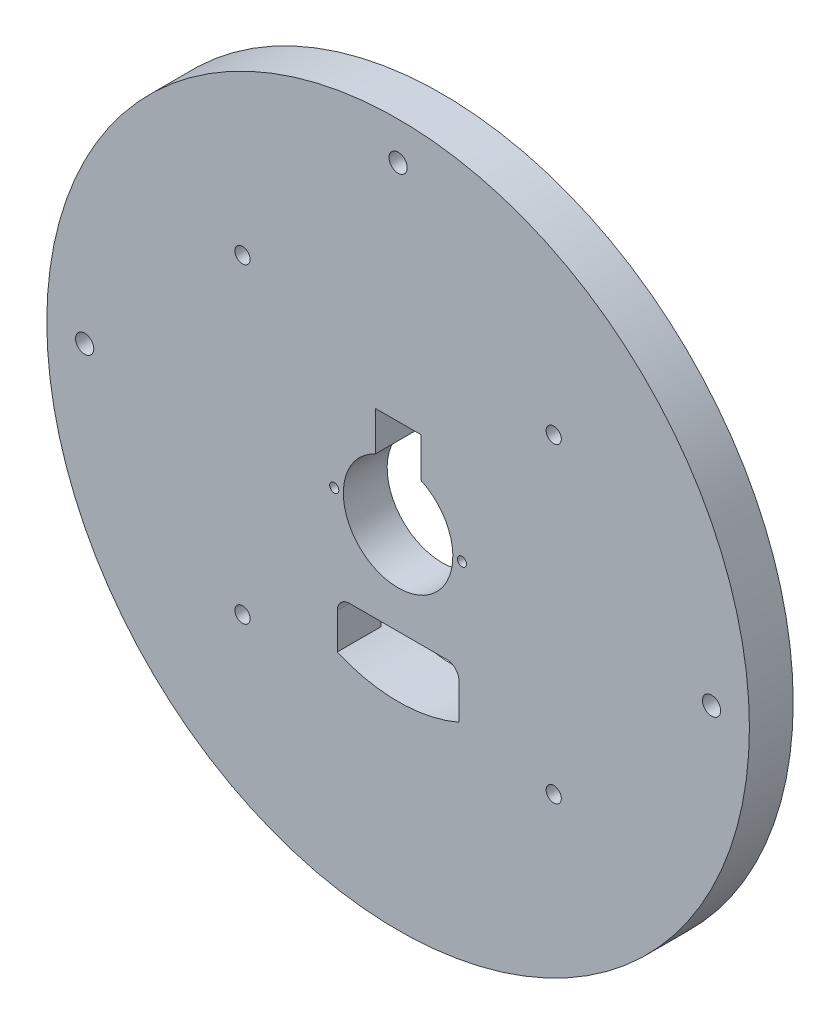
SolidWorks part; units mm, degrees
ref_plane "Front Plane" through (0, 0, 0) normal (0, 0, 1) x (1, 0, 0)
ref_plane "Top Plane" through (0, 0, 0) normal (0, 1, 0) x (1, 0, 0)
ref_plane "Right Plane" through (0, 0, 0) normal (1, 0, 0) x (0, 0, -1)
sketch "motorMount" plane through (0, 0, 0) normal (0, 0, 1) x (1, 0, 0)
  arc A26 (-115.3023, 6.7544) -> (-115.3023, -6.7544) centre (0, 0) ccw
  arc A27 (-115.3023, -6.7544) -> (115.3023, -6.7544) centre (0, 0) ccw
  arc A28 (115.3023, -6.7544) -> (115.3023, 6.7544) centre (0, 0) ccw
  arc A29 (115.3023, 6.7544) -> (-115.3023, 6.7544) centre (0, 0) ccw
  arc A30 (-115.3023, 6.7544) -> (-115.3023, -6.7544) centre (0, 0) ccw
  arc A31 (-115.3023, -6.7544) -> (115.3023, -6.7544) centre (0, 0) ccw
  arc A32 (115.3023, -6.7544) -> (115.3023, 6.7544) centre (0, 0) ccw
  arc A37 (115.3023, 6.7544) -> (-115.3023, 6.7544) centre (0, 0) ccw
  dimension "motorMountOffset" = 30
extrude "Boss-Extrude1" add sketch "motorMount" along normal blind 14.4
sketch "motorMountLockRings" plane through (0, 0, 0) normal (0, 0, -1) x (-1, 0, 0)
  line L0 (-55.2743, 5.1) -> (-55.1648, 5.1)
  line L1 (-55.2743, -5.1) -> (-55.1648, -5.1)
  line L2 (85.3537, 5.1) -> (85.4479, 5.1)
  line L5 (85.3537, -5.1) -> (85.4479, -5.1)
  line L14 (55.1648, 5.1) -> (55.2743, 5.1)
  line L15 (55.1648, -5.1) -> (55.2743, -5.1)
  line L16 (55.2743, 5.1) -> (85.3537, 5.1)
  line L17 (55.2743, 5.1) -> (85.3537, 5.1)
  line L18 (-85.3537, -5.1) -> (-85.4479, -5.1)
  line L19 (55.2743, -5.1) -> (85.3537, -5.1)
  line L20 (55.2743, -5.1) -> (85.3537, -5.1)
  line L21 (-85.3537, 5.1) -> (-85.4479, 5.1)
  line L22 (-85.3537, 5.1) -> (-55.2743, 5.1)
  line L23 (-85.3537, 5.1) -> (-55.2743, 5.1)
  line L25 (-85.3537, -5.1) -> (-55.2743, -5.1)
  line L26 (-85.3537, -5.1) -> (-55.2743, -5.1)
  circle A7 centre (0, 0) radius 50.4
  circle A16 centre (0, 0) radius 50.4
  arc A26 (90.4449, -5.2982) -> (90.4449, 5.2982) centre (0, 0) ccw
  arc A27 (55.1747, 4.991) -> (-55.1747, 4.991) centre (0, 0) ccw
  arc A28 (-90.4449, -5.2982) -> (90.4449, -5.2982) centre (0, 0) ccw
  arc A29 (-90.4449, 5.2982) -> (-90.4449, -5.2982) centre (0, 0) ccw
  arc A30 (55.1648, 5.1) -> (-55.1648, 5.1) centre (0, 0) ccw
  arc A31 (90.4449, 5.2982) -> (-90.4449, 5.2982) centre (0, 0) ccw
  arc A32 (-55.1747, -4.991) -> (55.1747, -4.991) centre (0, 0) ccw
  arc A33 (-55.1648, -5.1) -> (55.1648, -5.1) centre (0, 0) ccw
  arc A34 (90.4449, -5.2982) -> (90.4449, 5.2982) centre (0, 0) ccw
  arc A35 (-90.4449, -5.2982) -> (90.4449, -5.2982) centre (0, 0) ccw
  arc A36 (-90.4449, 5.2982) -> (-90.4449, -5.2982) centre (0, 0) ccw
  arc A37 (90.4449, 5.2982) -> (-90.4449, 5.2982) centre (0, 0) ccw
  arc A61 (85.4535, -5.0058) -> (85.4535, 5.0058) centre (0, 0) ccw
  arc A62 (-85.4535, -5.0058) -> (85.4535, -5.0058) centre (0, 0) ccw
  arc A63 (-85.4535, 5.0058) -> (-85.4535, -5.0058) centre (0, 0) ccw
  arc A64 (85.4535, 5.0058) -> (-85.4535, 5.0058) centre (0, 0) ccw
  arc A66 (-85.4479, -5.1) -> (85.4479, -5.1) centre (0, 0) ccw
  arc A68 (85.4479, 5.1) -> (-85.4479, 5.1) centre (0, 0) ccw
  dimension "D2" = 0.1
  dimension "D3" = 0.1
  dimension "D1" = 0.1
  dimension "D4" = 0.1
  dimension "D5" = 0.1
  dimension "D6" = 0.1
  dimension "D7" = 0.1
  dimension "D8" = 5.1
  dimension "D9" = 0.1
extrude "Boss-Extrude2" add sketch "motorMountLockRings" along normal blind 5
sketch "motorMountMotorCavity" plane through (0, 0, 0) normal (0, 0, -1) x (-1, 0, 0)
  line L0 (-7.5, 16.3631) -> (-7.5, 29.3631)
  line L1 (-7.5, 29.3631) -> (7.5, 29.3631)
  line L2 (7.5, 29.3631) -> (7.5, 16.3631)
  arc A0 (-7.5, 16.3631) -> (7.5, 16.3631) centre (0, 0) ccw
  dimension "motorDiameter" = 36
  dimension "motorConnectorWidth" = 15
  dimension "motorConnectorLength" = 13
extrude "Cut-Extrude1" cut sketch "motorMountMotorCavity" against normal blind 18.4
sketch "motorMountFaceplateHolePositions" plane through (0, 0, 0) normal (0, 0, -1) x (-1, 0, 0)
  line L0 (0, 0) -> (0, 40.4583) construction
  point P1 (-21, 0)
  point P2 (21, 0)
  dimension "motorFacePlateMountingHoleDistanceBetweenHoles" = 21
sketch "motorMountPelletThroughHole" plane through (0, 0, 0) normal (0, 0, -1) x (-1, 0, 0)
  line L0 (-20, -46.2619) -> (-20, -34.4)
  line L1 (-16, -30.4) -> (16, -30.4)
  line L2 (20, -34.4) -> (20, -46.2619)
  arc A2 (-20, -34.4) -> (-16, -30.4) centre (-16, -34.4) cw
  arc A3 (16, -30.4) -> (20, -34.4) centre (16, -34.4) cw
  circle A5 centre (0, 0) radius 50.4 construction
  arc A6 (-20, -46.2619) -> (20, -46.2619) centre (0, 0) ccw
  point P2 (0, -30.4)
  point P16 (0, -50.4)
  dimension "D1" = 4
  dimension "D4" = 20
  dimension "D3" = 40
extrude "Cut-Extrude2" cut sketch "motorMountPelletThroughHole" against normal through all contours L0 A2 L1 A3 L2 A6
hole_wizard "Ø5.0mm Dowel Hole1" positions "Sketch6" profile "Sketch7" hole size "Ø5.0" standard "ANSI Metric" end condition through all
sketch "Sketch6" plane through (0, 0, -16.7) normal (0, 0, -1) x (-1, 0, 0)
  point P0 (-51.1598, -51.1598)
  point P3 (51.1598, -51.1598)
  point P6 (51.1598, 51.1598)
  point P9 (-51.1598, 51.1598)
sketch "Sketch7" plane through (51.1598, -51.1598, -16.7) normal (1, 0, 0) x (0, 1, 0)
  line L0 (0, 0) -> (0, 31.1)
  line L1 (0, 31.1) -> (2.5, 31.1)
  line L2 (2.5, 31.1) -> (2.5, 0)
  line L3 (2.5, 0) -> (0, 0)
  line L4 (0, -6.35) -> (0, 107.95) construction
  dimension "Thru Hole Dia." = 5
  dimension "Thru Hole Depth" = 31.1
hole_wizard "Ø3.0mm Dowel Hole3" positions "Sketch10" profile "Sketch11" hole size "Ø3.0" standard "ANSI Metric" end condition through all
sketch "Sketch10" plane through (0, 0, 0) normal (0, 0, -1) x (-1, 0, 0)
  point P0 (-21, 0)
  point P3 (21, 0)
sketch "Sketch11" plane through (21, 0, 0) normal (1, 0, 0) x (0, 1, 0)
  line L0 (0, 0) -> (0, 14.4)
  line L1 (0, 14.4) -> (1.5, 14.4)
  line L2 (1.5, 14.4) -> (1.5, 0)
  line L3 (1.5, 0) -> (0, 0)
  line L4 (0, -6.35) -> (0, 107.95) construction
  dimension "Thru Hole Dia." = 3
  dimension "Thru Hole Depth" = 14.4
hole_wizard "Ø6.0mm Dowel Hole4" positions "Sketch12" profile "Sketch13" hole size "Ø6.0" standard "ANSI Metric" end condition through all
sketch "Sketch12" plane through (0, 0, 24.4) normal (0, 0, 1) x (1, 0, 0)
  point P0 (-103.05, 0)
  point P3 (103.05, 0)
  point P6 (0, 103.05)
sketch "Sketch13" plane through (-103.05, 0, 24.4) normal (1, 0, 0) x (0, -1, 0)
  line L0 (0, 0) -> (0, 29.4)
  line L1 (0, 29.4) -> (3, 29.4)
  line L2 (3, 29.4) -> (3, 0)
  line L3 (3, 0) -> (0, 0)
  line L4 (0, -6.35) -> (0, 107.95) construction
  dimension "Thru Hole Dia." = 6
  dimension "Thru Hole Depth" = 29.4
equation "\"D1@Boss-Extrude1\"=\"motorMountHeight\""
equation "\"pelletWidth\"= 13mm'The Width of the pellet to be dispensed"
equation "\"pelletLength\"= 26mm'The length of the pellet to be dispensed"
equation "\"pelletThickness\"= 13mm'The Thickness of the pellet to be dispensed"
equation "\"pelletRadius\"= 10mm'The roundness / radius of the pellet to be dispensed"
equation "\"rotatingPlateDiameter\"= 100mm'the diameter of the rotating plate"
equation "\"rotatingPlateHeight\"= (\"pelletThickness\"*0.9)'The thickness of the rotating plate"
equation "\"rotatingPlateDiameterAllowance\"= 0.5mm'Allowance around the edge of the rotating plate"
equation "\"hopperBaseChamferAngle\"= 60deg'Angle of the chamfer of the Hopper base Toward the plate"
equation "\"hopperBaseLipOverhang\"= 5mm'The overhang amount of the hopper base lip"
equation "\"hopperBaseLipDepth\"= 5mm'The depth of the hopper base's overhang lip"
equation "\"hopperBaseRearNotchHeight\"= 8mm'The height of the rear snap-lock notch on the hopper base"
equation "\"hopperBaseRearNotchWidth\"= 8mm'The width of the rear snap-lock notch on the hopper base"
equation "\"hopperTankWallThickness\"= 5mm'The wall thickness of the hopper tank where pellet reserve will be stored"
equation "\"hopperTankDiameter\"= ( \"rotatingPlateDiameter\"*1.8 )'**Must be greater than \"rotatingPlateDiameter\" -- The inner diameter of the hopper tank where pellet reserve will be stored"
equation "\"hopperTankHeight\"= 200mm'The height of the hopper tank where pellet reserve will be stored"
equation "\"motorMountHeight\"= (\"motorHeight\" + \"motorFacePlateThickness\" + 0mm)'The height / thickness of the motor mount part"
equation "\"motorDiameter\"= 35mm'The Diameter of the main motor unit"
equation "\"motorHeight\"= 13.4mm'The height of the main motor unit"
equation "\"motorFacePlateLength\"= 50mm'The length of the motor faceplate"
equation "\"motorFacePlateWidth\"= 10mm'The width of the motor faceplate"
equation "\"motorFacePlateThickness\"= 1mm'The thickness of the motor faceplate"
equation "\"motorFacePlateCenterRadius\"= 20mm'The rounding radius of the motor faceplate center"
equation "\"motorFacePlateEndRadius\"= 10mm'The rounding radius of the motor faceplate ends"
equation "\"motorFacePlateMountingHoleDiameter\"= 6mm'The diameter of the motor faceplate's mounting holes"
equation "\"motorFacePlateMoutingHoleDistanceBetweenHoles\"= 42mm'The distance between the center of the mounting holes"
equation "\"motorSpindleDiameter\"= 2mm'The diameter of the motor spindle"
equation "\"motorSpindleFlatFaceLength\"= 1.5mm'The length of the flat face of the motor spindle"
equation "\"motorSpindleHeight\"= 9mm'The height of the motor spindle from the face of the motor"
equation "\"motorSpindleMountDiameter\"= 12mm'The diameter of the raised mount section of the motor where the spindle is attached"
equation "\"motorSpindleMountHeight\"= 1.5mm'The height of the raised mount section of the motor where the spindle is attached"
equation "\"motorDiameter@motorMountMotorCavity\" = \"motorDiameter\" + 1"
equation "\"D1@Cut-Extrude1\"=\"motorHeight\"+5"
equation "\"motorConnectorWidth\"= 10mm'The width of the motor's electrical cable connector"
equation "\"motorConnectorLength\"= 8mm'The length of the motor's electrical cable connector"
equation "\"motorConnectorHeight\"= 5mm'The height of the motor's electrical cable connector"
equation "\"motorConnectorWidth@motorMountMotorCavity\" = \"motorConnectorWidth\" + 5"
equation "\"motorConnectorLength@motorMountMotorCavity\" = \"motorConnectorLength\" + 5"
equation "\"motorFacePlateMountingHoleDistanceBetweenHoles@motorMountFaceplateHolePositions\" = \"motorFacePlateMoutingHoleDistanceBetweenHoles\" / 2"
equation "\"motorMountOffset\"= 30mm'The distance offset of the motor mount part from the hopper tank's outer edge"
equation "\"motorMountOffset@motorMount\" = \"motorMountOffset\""
equation "\"D1@Boss-Extrude2\"=\"hopperBaseLipDepth\""
equation "\"hopperBaseLockNotchWidth\"= 10mm'The width of the hopper base \"lock\" notch to prevent rotation"
equation "\"hopperBaseLockNotchHeight\"= 10mm'The height of the hopper base \"lock\" notch to prevent rotation"
equation "\"generalFittingTolerance\"= 0.1mm'The general fitting tolerance between contacting parts"
equation "\"D2@motorMountLockRings\" = \"generalFittingTolerance\""
equation "\"D1@motorMountLockRings\" = \"generalFittingTolerance\""
equation "\"D3@motorMountLockRings\" = \"generalFittingTolerance\""
equation "\"D6@motorMountLockRings\" = \"generalFittingTolerance\""
equation "\"D7@motorMountLockRings\" = \"generalFittingTolerance\""
equation "\"D5@motorMountLockRings\" = \"generalFittingTolerance\""
equation "\"D4@motorMountLockRings\" = \"generalFittingTolerance\""
equation "\"D9@motorMountLockRings\" = \"generalFittingTolerance\""
equation "\"rotatingPlateAgitatorDiameter\"= ( \"rotatingPlateDiameter\"-((\"pelletWidth\"*1.3)*2.5) )'The diameter of the \"agitator\" section of the rotating plate"
equation "\"rotatingPlateAgitatorHeight\"= 80mm'The height of the \"agitator\" section of the rotating plate"
equation "\"rotatingPlateAgitatorBladeThickness\"= 4mm'The thickness of the blade on the \"agitator\" section of the rotating plate"
equation "\"rotatingPlateAgitatorBladeDistance\"= ( (\"rotatingPlateAgitatorDiameter\"+ 20mm) - (\"rotatingPlateAgitatorDiameter\") )'The distance offset of the blade from the surface of the \"agitator\" section of the rotating plate"
equation "\"rotatingPlateAgitatorBladeBottomGap\"= ( \"pelletThickness\"*1.2 )'The gap between the bottom of the blade and the base of the plate on the \"agitator\" section of the rotating plate"
equation "\"rotatingPlateAgitatorBladesNumber\"= ( 3 )'The number of blades on the \"agitator\" section of the rotating plate"
equation "\"hopperTankCoverThickness\"= 10mm'The thickness of the Hopper Tank's cover"
equation "\"hopperTankCoverHandleLength\"= 60mm'The length of the handles on the hopper tank cover"
equation "\"hopperTankCoverHandleWidth\"= 20mm'The width of the handles on the hopper tank cover, defined as the offset from the cover's main edge"
equation "\"D4@motorMountPelletThroughHole\" = \"motorMountPelletThroughHoleWidth\""
equation "\"D3@motorMountPelletThroughHole\" = \"motorMountPelletThroughHoleLength\""
equation "\"D8@motorMountLockRings\" = \"hopperBaseLipOverhang\" + \"generalFittingTolerance\""
equation "\"hopperBaseInnerDiameter\"= (\"rotatingPlateDiameter\") + (\"rotatingPlateDiameterAllowance\"*2)'Diameter of the Base of the hopper where it meets the motor mount + rotating plate"
equation "\"hopperBaseOuterDiameter\"= (\"hopperBaseInnerDiameter\" + (\"hopperTankWallThickness\"*2) + 60mm)'Diameter of the Base of the hopper where it meets the motor mount + rotating plate"
equation "\"motorMountPelletThroughHoleLength\"= 40mm'The length of the pellet throughhole that routes through the motor mount and other parts"
equation "\"motorMountPelletThroughHoleWidth\"= 20mm'The width of the pellet throughhole that routes through the motor mount and other parts"
equation "\"rotatingPlatePelletSlotLength\"= \"pelletLength\"*1.3'The length of the slot where a pellet will be captured"
equation "\"rotatingPlatePelletSlotWidth\"= \"pelletWidth\"*1.3'The width of the slot where a pellet will be captured"
equation "\"rotatingPlateNumberOfPelletSlots\"= ( (2*pi*(\"rotatingPlateDiameter\"/2)) / ((\"rotatingPlatePelletSlotLength\"*1.1)*3) )'The maximum number of pellet slots allows in the rotating plate for proper spacing"
equation "\"rotatingPlateAgitatorTopRoundingRadius\"= 6mm'The rounding radius of the top of the \"agitator\" section of the rotating plate"
equation "\"hopperBasePelletBlockerMountingSlotWidth\"= 5mm'The width of the pellet blocker mounting slot on the hopper base"
equation "\"hopperBasePelletBlockerMountingSlotOffsetFromTopOfChamfer\"= 15mm'The distance offset of the top of the pellet blocker mounting slot from the top of the hopper base chamfer"
equation "\"hopperBasePelletBlockerMountingSlotOffsetFromBottomOfChamfer\"= 10mm'The distance offset of the bottom of the pellet blocker mounting slot from the bottom of the hopper base chamfer"
equation "\"irBeamUnitLength\"=20mm'The legth of the IR beam unit"
equation "\"irBeamUnitWidth\"=10mm'The width of the IR beam unit"
equation "\"irBeamUnitHeight\"=8mm'The height of the IR beam unit"
equation "\"irBeamUnitSlotWidth\"=2.03mm'The width of the slots on the outside of the IR beam unit"
equation "\"irBeamUnitSlotLength\"=5.10mm'The length of the slots of the outside of the IR beam unit"
equation "\"irBeamUnitSlotDepth\"=0.76mm'The depth of the slots on the outside of the IR beam unit"
equation "\"irBeamUnitSlotChamferAngle\"=45deg'The angle of the \"end\" of the slot on the outside of the IR beam unit"
equation "\"irBeamUnitSideSlotsDistanceFromBottom\"=3.98mm'The distance of the side slots on the outside of the IR beam unit from the bottom edge of the unit"
equation "\"irBeamUnitMountHoleDistanceFromBottom\"=5mm'The distance of the center mounting throughhole of the IR beam unit from the bottom edge of the unit"
equation "\"irBeamUnitMountHoleDiameter\"=2.40mm'The diameter of the center mounting throughhole of the IR beam unit"
equation "\"irBeamUnitMountHoleChamferDiameter\"=5.30mm'The diameter of the chamfer of the center mounting throughole of the IR beam unit"
equation "\"irBeamUnitMountHoleChamferDepth\"=2.65mm'The depth of the chamfer of the center mounting throughole of the IR beam unit"
equation "\"irBeamUnitLEDDistanceFromBottom\"=15mm'The distance of the center of the LED from the bottom edge of the IR beam unit"
equation "\"irBeamUnitLEDMountDiameter\"=8mm'The diameter of the LED mounting base of the IR beam unit"
equation "\"irBeamUnitLEDMountHeight\"=1.02mm'The height of the LED mounting base of the IR beam unit"
equation "\"irBeamUnitLEDDiameter\"=3.00mm'The diameter of the LED of the IR beam unit"
equation "\"irBeamUnitLEDFlatSectionHeight\"=0.65mm'The height of the \"flat\" section of the LED of the IR beam unit"
equation "\"irBeamUnitLEDDomeSectionDiameter\"=\"irBeamUnitLEDDiameter\"'The diameter of the \"domed\" section of the LED of the IR beam unit"
equation "\"irBeamUnitMountingPlateThickness\"=2mm'The thickness of the IR beam unit mounting plate"
equation "\"irBeamUnitMountingPlateAdjustmentSlotLength\"=10mm'The length of the variable/adjustable mounting slot of the IR beam unit mounting plate"
equation "\"pelletBlockerBaseWidth\"= (\"rotatingPlatePelletSlotWidth\"+\"rotatingPlateDiameterAllowance\")*1.1'The width of the base of the pellet blocker where it meets the rotating plate & pellet slot"
equation "\"pelletBlockerBaseLength\"= \"rotatingPlatePelletSlotLength\"*1.1'The length of the base of the pellet blocker where it meets the rotating plate & pellet slot"
equation "\"pelletBlockerBaseRoundingRadius\"= \"pelletWidth\"*0.5'The rounding radius of the base of the pellet blocker where it meets the rotating plate & pellet slot"
equation "\"pelletBlockerBaseHeight\"= \"rotatingPlateAgitatorBladeBottomGap\"*0.75'The height of the base of the pellet blocker where it meets the rotating plate & pellet slot"
equation "\"pelletBlockerNeckLength\"= 50mm'The length of the neck of the pellet blocker"
equation "\"pelletBlockerNeckTopRoundingRadius\"=2mm'The rounding radius of the top of the neck of the pellet blocker"
equation "\"pelletOutletTrackMountingPlateThickness\"= 2mm'The thickness of the Pellet Outlet Track Mounting Plate"
equation "\"pelletOutletTrackMountingPlateHingeHeight\"= (\"irBeamUnitWidth\" + \"irBeamUnitMountingPlateThickness\" + 2mm )'The height of the bottom of the hinge of the Pellet Outlet Mounting Plate"
equation "\"pelletOutletTrackMountingPlateHingeDiameter\"= 6mm'The inner diameter of the hinge on the Pellet Outlet Mounting Plate"
equation "\"pelletOutletTrackMountingPlateHingeOffsetFromHoleDistance\"= (\"pelletOutletTrackMountingPlateHingeDiameter\" + \"pelletOutletTrackMountingPlateThickness\" + 4mm)'The distance offset of the hinge of the Pellet Outlet Mounting Plate from the plate's mounting hole position"
equation "\"pelletOutletTrackHingeWidth\"= 10mm'The width of the pellet outlet track's hinge which mates with the hinge on the mounting plate"
equation "\"pelletOutletTrackHingeOffsetFromIRBeamUnitEdge\"= 6mm'The distance offset of the pelletOutletTrack's mating hinge from the edge of the IR Beam Unit"
equation "\"pelletOutletTrackEndingWidth\"= 50mm'The width of the pellet outlet Track at the end of the Track"
equation "\"pelletOutletTrackEndingLength\"= 30mm'The length of pellet outlet Track at the end of the Track"
equation "\"pelletOutletTrackWallHeight\"= 15mm'The height of the side walls of the pellet outlet Track"
equation "\"pelletOutletTrackThickness\"= 2mm'The thickness of the pellet outlet Track"
equation "\"baseStandMountingFaceHeight\"= 10mm'The height / thickness of the mounting face between the Base Stand and the Motor Mount parts"
equation "\"baseStandOpeningAngle\"= 55deg'The angle of the opening in the front of the Base Stand to allow for unobstructed pellet outlet"
equation "\"baseStandWallThickness\"= 10mm'The wall thickness of the Base Stand"
equation "\"baseStandHeight\"= 100mm'The overall height of the Base Stand part"
equation "\"baseStandFootDiameterOffset\"= 40mm'The distance offset of the Base Stand's foot ring"
equation "\"baseStandFootHeight\"= 20mm'The height / thickness of the Base Stand's foot ring"
